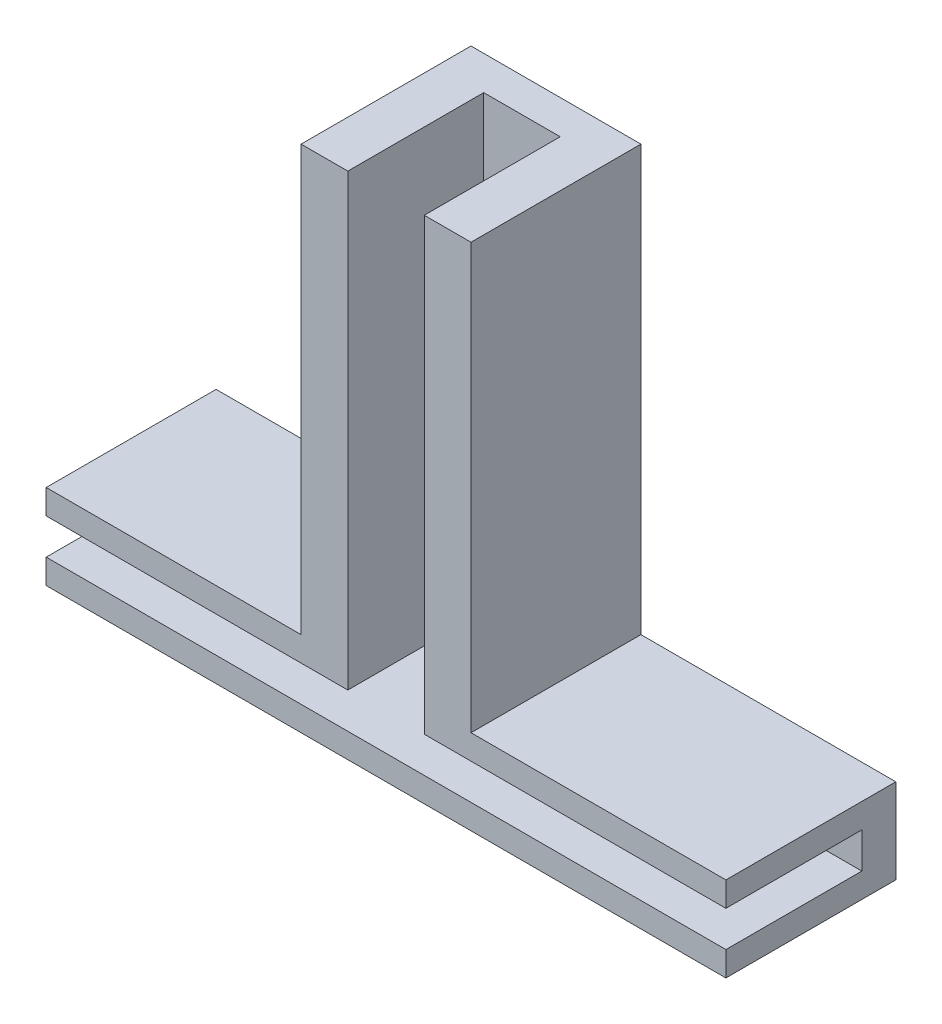
SolidWorks part; units mm, degrees
ref_plane "Front Plane" through (0, 0, 0) normal (0, 0, 1) x (1, 0, 0)
ref_plane "Top Plane" through (0, 0, 0) normal (0, 1, 0) x (1, 0, 0)
ref_plane "Right Plane" through (0, 0, 0) normal (1, 0, 0) x (0, 0, -1)
sketch "Sketch1" plane through (0, 0, 0) normal (0, 1, 0) x (1, 0, 0)
  line L1 (-20, -5) -> (20, -5)
  line L2 (-20, -5) -> (-20, 5)
  line L3 (-20, 5) -> (20, 5)
  line L4 (20, -5) -> (20, 5)
  line L5 (-20, -5) -> (20, 5) construction
  line L6 (-20, 5) -> (20, -5) construction
  point P0 (0, 0)
  dimension "D1" = 40
  dimension "D2" = 10
extrude "Boss-Extrude1" add sketch "Sketch1" along normal blind 5
sketch "Sketch2" plane through (20, 0, 0) normal (1, 0, 0) x (0, 0, -1)
  line L0 (3, 3.55) -> (3, 1.45)
  line L3 (-5, 1.45) -> (3, 1.45)
  line L4 (-5, 3.55) -> (3, 3.55)
  line L5 (5, 5) -> (5, 0) construction
  line L6 (-5, 5) -> (-5, 0) construction
  line L7 (-5, 3.55) -> (-5, 1.45)
  dimension "D1" = 2
extrude "Cut-Extrude2" cut sketch "Sketch2" against normal through all
sketch "Sketch3" plane through (0, 0, -5) normal (0, 0, -1) x (-1, 0, 0)
  line L0 (-5, 30) -> (5, 30)
  line L1 (-5, 5) -> (5, 5)
  line L3 (5, 0) -> (5, 30)
  line L4 (-5, 0) -> (-5, 30)
  line L5 (-5, 0) -> (5, 0)
  line L6 (-20, 5) -> (20, 5) construction
  line M7 (20, 5) -> (-20, 5)
extrude "Boss-Extrude2" add sketch "Sketch3" against normal up to vertex (10 mm away) contours L4 L3 L0 M7 up to point (20, 5, 5)
sketch "Sketch4" plane through (0, 0, 5) normal (0, 0, 1) x (1, 0, 0)
  line L0 (0, 30) -> (0, 3.55)
  line L1 (5, 30) -> (-5, 30) construction
  line L2 (-20, 3.55) -> (20, 3.55) construction
  line L3 (-2.25, 30) -> (-2.25, 3.55)
  line L4 (2.25, 30) -> (2.25, 3.55)
  line L6 (-2.25, 30) -> (2.25, 30)
  line L7 (-2.25, 30) -> (-2.25, 3.55)
  line L8 (-2.25, 3.55) -> (2.25, 3.55)
  line L9 (2.25, 30) -> (2.25, 3.55)
  line M3 (-20, 3.55) -> (20, 3.55)
  line M7 (5, 30) -> (-5, 30)
  dimension "D1" = 2.25
  dimension "D2" = 2.25
extrude "Cut-Extrude3" cut sketch "Sketch4" against normal up to vertex (8 mm away) contours L3 L0 M7 M3 | L4 L0 M7 M3 up to point (20, 3.55, -3)
